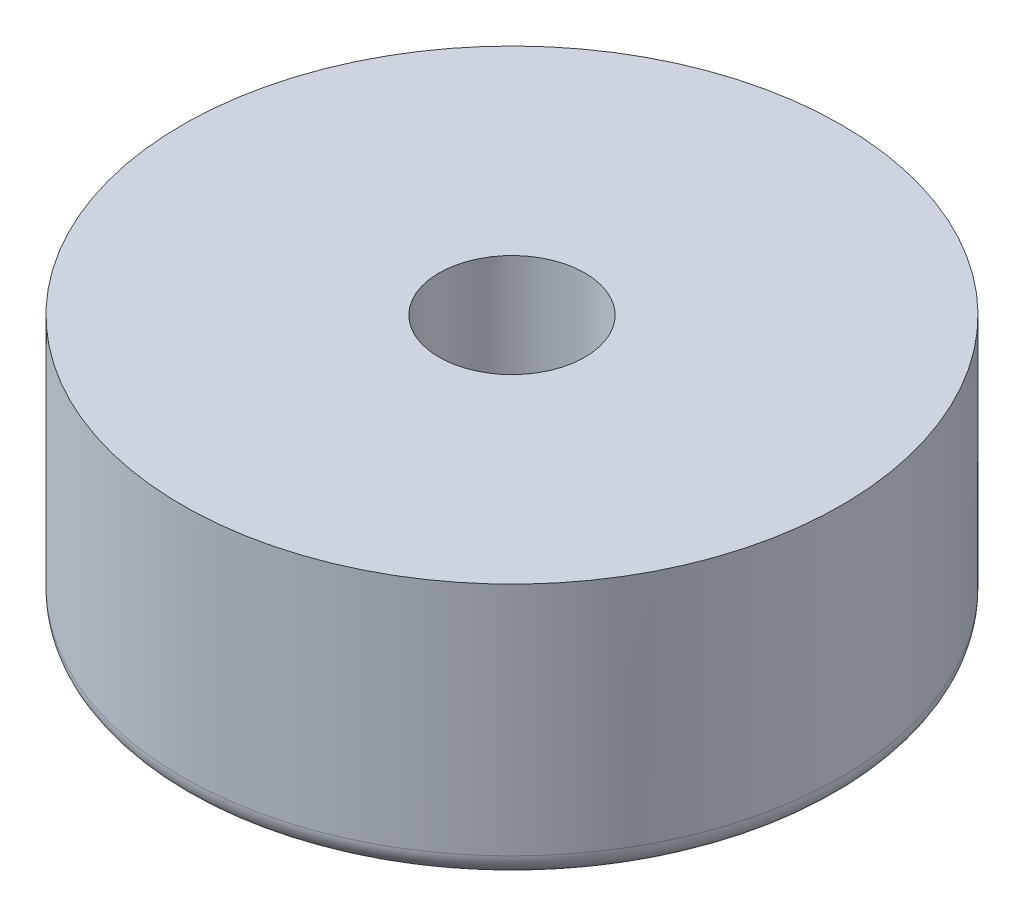
SolidWorks part; units mm, degrees
ref_plane "Front Plane" through (0, 0, 0) normal (0, 0, 1) x (1, 0, 0)
ref_plane "Top Plane" through (0, 0, 0) normal (0, 1, 0) x (1, 0, 0)
ref_plane "Right Plane" through (0, 0, 0) normal (1, 0, 0) x (0, 0, -1)
sketch "Sketch1" plane through (0, 0, 0) normal (0, 0, 1) x (1, 0, 0)
  line L0 (0, 0) -> (0, 3.8107) construction
  line L1 (-1.55, 0) -> (-7, 0)
  line L2 (-7, 0) -> (-7, -5.5)
  line L3 (-7, -5.5) -> (-4, -5.5)
  line L4 (-4, -5.5) -> (-4, -3.3738)
  line L5 (-4, -3.3738) -> (-1.55, -3.3738)
  line L6 (-1.55, -3.3738) -> (-1.55, 0)
  dimension "D1" = 14
  dimension "D2" = 5.5
  dimension "D3" = 3.1
  dimension "D4" = 8
revolve "Revolve1" add sketch "Sketch1" angle 360 about L0
fillet "Fillet1" radius 0.5 2 edges at (0, -5.5, -7) (0, -5.5, -4)
